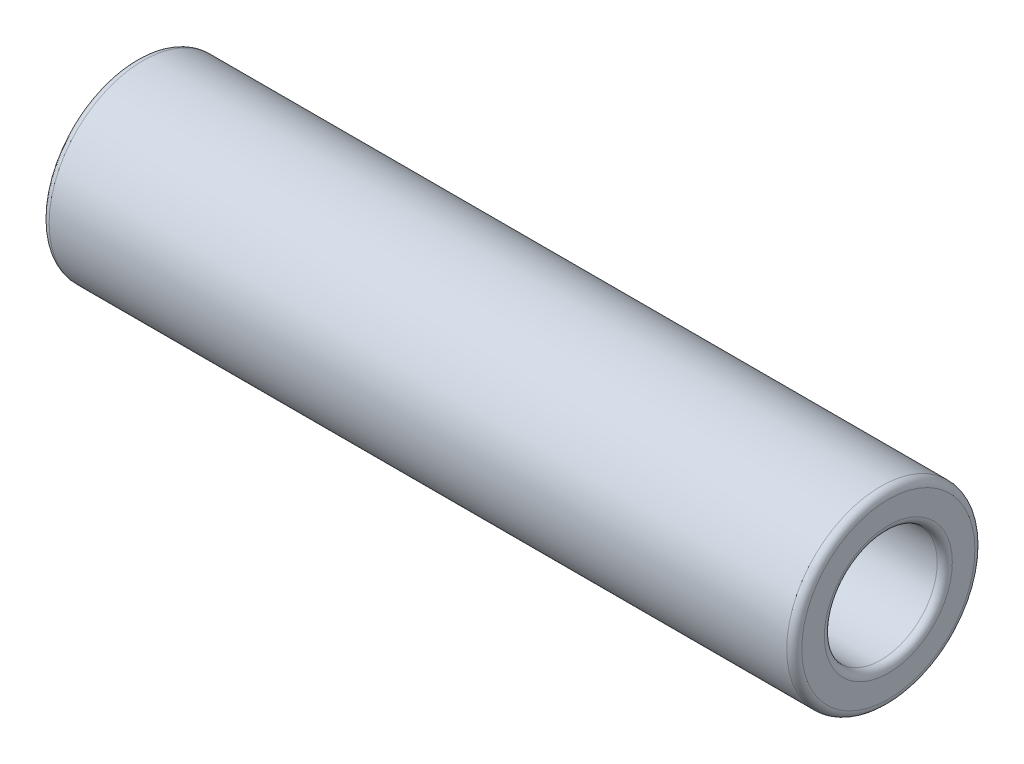
SolidWorks part; units mm, degrees
ref_plane "Front Plane" through (0, 0, 0) normal (0, 0, 1) x (1, 0, 0)
ref_plane "Top Plane" through (0, 0, 0) normal (0, 1, 0) x (1, 0, 0)
ref_plane "Right Plane" through (0, 0, 0) normal (1, 0, 0) x (0, 0, -1)
sketch "Sketch1" plane through (0, 0, 0) normal (1, 0, 0) x (0, 0, -1)
  circle A0 centre (0, 0) radius 95.25
  circle A1 centre (0, 0) radius 158.75
  dimension "D1" = 317.5
  dimension "D2" = 190.5
extrude "Boss-Extrude1" add sketch "Sketch1" along normal blind 1270
fillet "Fillet1" radius 12.7 2 edges at (1270, 0, -95.25) (1270, 0, -158.75)
fillet "Fillet2" radius 12.7 2 edges at (0, 0, -95.25) (0, 0, -158.75)
